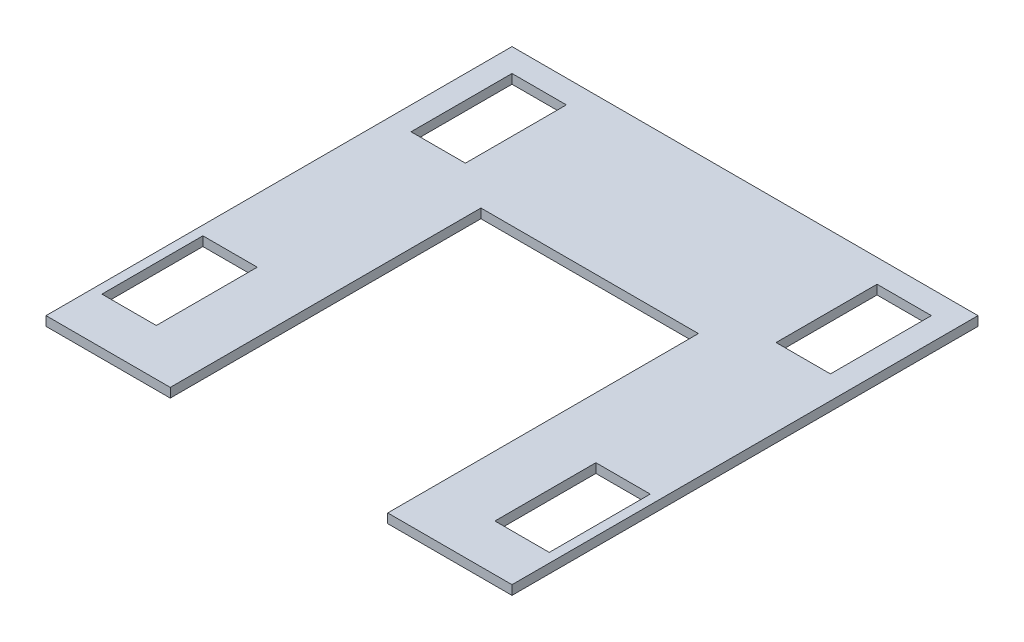
SolidWorks part; units mm, degrees
ref_plane "Front Plane" through (0, 0, 0) normal (0, 0, 1) x (1, 0, 0)
ref_plane "Top Plane" through (0, 0, 0) normal (0, 1, 0) x (1, 0, 0)
ref_plane "Right Plane" through (0, 0, 0) normal (1, 0, 0) x (0, 0, -1)
sketch "Sketch1" plane through (0, 0, 0) normal (0, 1, 0) x (1, 0, 0)
  line L0 (0, 0) -> (80, 0)
  line L2 (0, 0) -> (0, 300)
  line L3 (0, 300) -> (300, 300)
  line L4 (300, 0) -> (300, 300)
  line L5 (80, 0) -> (80, 200)
  line L6 (80, 200) -> (220, 200)
  line L7 (220, 200) -> (220, 0)
  line L8 (220, 0) -> (300, 0)
  line L10 (15, 285) -> (50, 285)
  line L11 (15, 285) -> (15, 220)
  line L12 (15, 220) -> (50, 220)
  line L13 (50, 285) -> (50, 220)
  line L14 (250, 285) -> (285, 285)
  line L15 (250, 285) -> (250, 220)
  line L16 (250, 220) -> (285, 220)
  line L17 (285, 285) -> (285, 220)
  line L18 (6, 30) -> (41, 30)
  line L19 (6, 30) -> (6, 95)
  line L20 (6, 95) -> (41, 95)
  line L21 (41, 30) -> (41, 95)
  line L22 (294, 30) -> (259, 30)
  line L23 (294, 30) -> (294, 95)
  line L24 (294, 95) -> (259, 95)
  line L25 (259, 30) -> (259, 95)
  dimension "D1" = 300
  dimension "D2" = 300
  dimension "D3" = 30
  dimension "D4" = 200
  dimension "D5" = 140
  dimension "D6" = 15
  dimension "D7" = 15
  dimension "D8" = 35
  dimension "D9" = 65
  dimension "D10" = 35
  dimension "D11" = 15
  dimension "D12" = 6
  dimension "D13" = 35
  dimension "D14" = 35
  dimension "D15" = 65
  dimension "D16" = 65
  dimension "D17" = 6
  dimension "D18" = 30
extrude "Boss-Extrude1" add sketch "Sketch1" along normal blind 6
